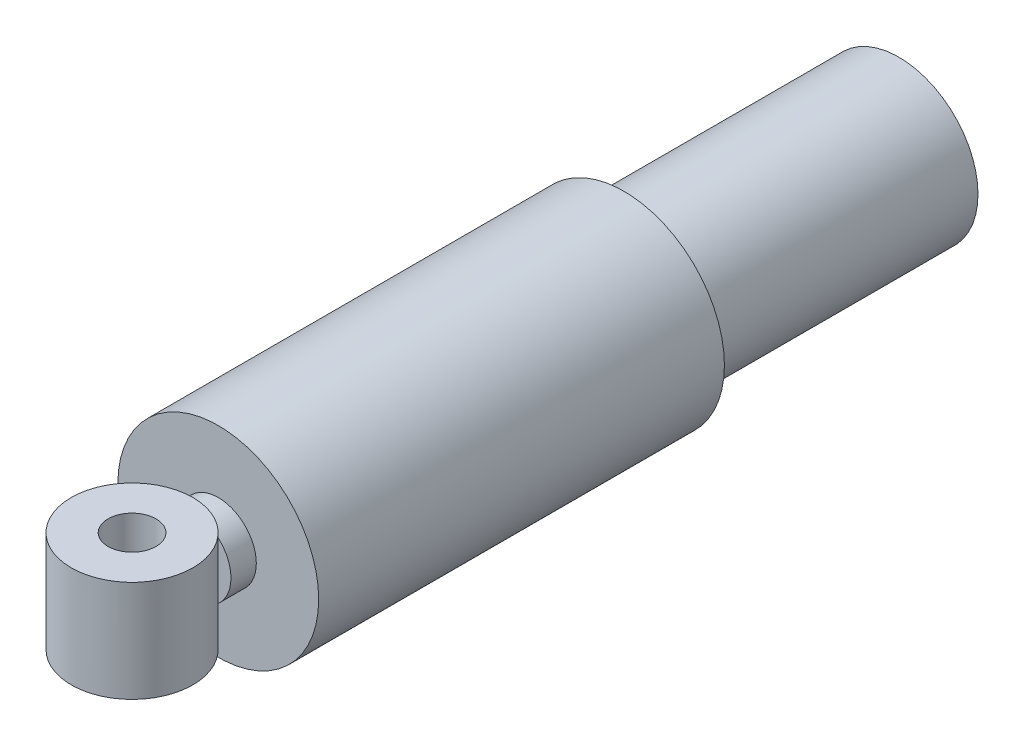
SolidWorks part; units mm, degrees
ref_plane "Front Plane" through (0, 0, 0) normal (0, 0, 1) x (1, 0, 0)
ref_plane "Top Plane" through (0, 0, 0) normal (0, 1, 0) x (1, 0, 0)
ref_plane "Right Plane" through (0, 0, 0) normal (1, 0, 0) x (0, 0, -1)
sketch "Sketch1" plane through (0, 0, 0) normal (0, 0, 1) x (1, 0, 0)
  circle A0 centre (0, 0) radius 19.812
  dimension "D1" = 39.624
extrude "Boss-Extrude1" add sketch "Sketch1" along normal blind 68.834
sketch "Sketch2" plane through (0, 0, 68.834) normal (0, 0, 1) x (1, 0, 0)
  circle A0 centre (0, 0) radius 25.146
  dimension "D1" = 50.292
extrude "Boss-Extrude2" add sketch "Sketch2" along normal blind 101.6
sketch "Sketch3" plane through (0, 0, 170.434) normal (0, 0, 1) x (1, 0, 0)
  circle A0 centre (0, 0) radius 9.525
  dimension "D1" = 19.05
extrude "Boss-Extrude3" add sketch "Sketch3" along normal blind 6.35
sketch "Sketch5" plane through (0, 0, 0) normal (0, 1, 0) x (1, 0, 0)
  line L0 (-9.525, -176.784) -> (9.525, -176.784) construction
  line L1 (-9.525, -176.784) -> (9.525, -176.784)
  line L2 (0, -176.784) -> (0, -192.024)
  circle A0 centre (0, -192.024) radius 15.24
  dimension "D1" = 15.24
extrude "Boss-Extrude4" add sketch "Sketch5" along normal blind 12.7 separate body
sketch "Sketch6" plane through (0, 0, 0) normal (0, -1, 0) x (1, 0, 0)
  circle A0 centre (0, 192.024) radius 15.24
  dimension "D1" = 30.48
extrude "Boss-Extrude5" add sketch "Sketch6" along normal blind 12.7 contours A0
sketch "Sketch7" plane through (0, 12.7, 0) normal (0, 1, 0) x (1, 0, 0)
  circle A0 centre (0, -192.024) radius 6.0007
  dimension "D1" = 12.0015
extrude "Cut-Extrude1" cut sketch "Sketch7" against normal through all
